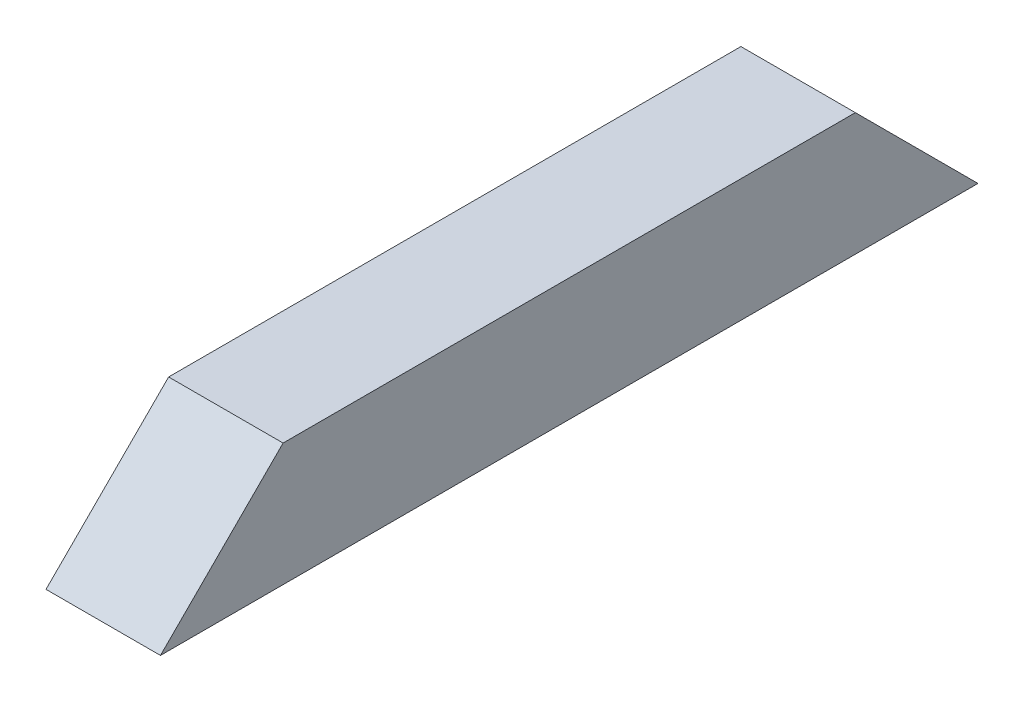
SolidWorks part; units mm, degrees
material "1060 Alloy"
ref_plane "Front Plane" through (0, 0, 0) normal (0, 0, 1) x (1, 0, 0)
ref_plane "Top Plane" through (0, 0, 0) normal (0, 1, 0) x (1, 0, 0)
ref_plane "Right Plane" through (0, 0, 0) normal (1, 0, 0) x (0, 0, -1)
sketch "Sketch1" plane through (0, 0, 0) normal (0, 1, 0) x (1, 0, 0)
  line L1 (0, 0) -> (8.89, 0)
  line L2 (0, 0) -> (0, 63.5)
  line L3 (0, 63.5) -> (8.89, 63.5)
  line L4 (8.89, 0) -> (8.89, 63.5)
  dimension "D1" = 8.89
  dimension "D2" = 63.5
extrude "Boss-Extrude1" add sketch "Sketch1" along normal blind 9.525
sketch "Sketch2" plane through (8.89, 0, 0) normal (1, 0, 0) x (0, 0, -1)
  line L0 (0, 0) -> (9.525, 9.525)
  line L1 (0, 9.525) -> (63.5, 9.525) construction
  line L2 (9.525, 9.525) -> (0, 9.525)
  line L4 (63.5, 0) -> (63.5, 9.525)
  line L5 (63.5, 9.525) -> (53.975, 9.525)
  line L6 (53.975, 9.525) -> (63.5, 0)
  line M6 (63.5, 0) -> (63.5, 9.525)
  line M7 (63.5, 9.525) -> (0, 9.525)
  line M8 (0, 9.525) -> (0, 0)
  dimension "D1" = 9.525
  dimension "D2" = 9.525
extrude "Cut-Extrude1" cut sketch "Sketch2" against normal through all contours L0 M8 M7 | L6 M7 M6
